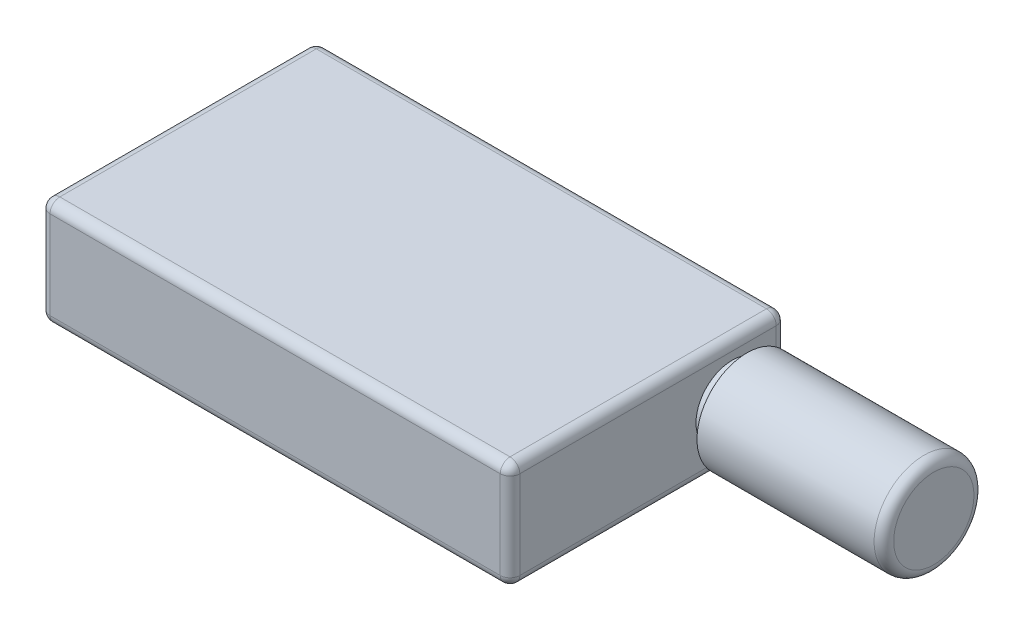
SolidWorks part; units mm, degrees
ref_plane "Front Plane" through (0, 0, 0) normal (0, 0, 1) x (1, 0, 0)
ref_plane "Top Plane" through (0, 0, 0) normal (0, 1, 0) x (1, 0, 0)
ref_plane "Right Plane" through (0, 0, 0) normal (1, 0, 0) x (0, 0, -1)
sketch "Sketch1" plane through (0, 0, 0) normal (0, 1, 0) x (1, 0, 0)
  line L1 (0, 0) -> (48, 0)
  line L2 (0, 0) -> (0, 28.2)
  line L3 (0, 28.2) -> (48, 28.2)
  line L4 (48, 0) -> (48, 28.2)
  dimension "D1" = 28.2
  dimension "D2" = 48
extrude "Boss-Extrude1" add sketch "Sketch1" along normal blind 11
sketch "Sketch2" plane through (48, 0, 0) normal (1, 0, 0) x (0, 0, -1)
  line L0 (28.2, 11) -> (28.2, 0) construction
  circle A0 centre (22.7, 5.5) radius 3.7
  point P5 (28.2, 5.5)
  dimension "D1" = 7.4
  dimension "D2" = 5.5
extrude "Boss-Extrude2" add sketch "Sketch2" along normal blind 1.5
sketch "Sketch3" plane through (49.5, 0, 0) normal (1, 0, 0) x (0, 0, -1)
  circle A0 centre (22.7, 5.5) radius 5.1
  dimension "D1" = 10.2
extrude "Boss-Extrude3" add sketch "Sketch3" along normal blind 19.1
fillet "Fillet1" radius 1 12 edges at (48, 0, -14.1) (48, 5.5, -28.2) (24, 0, -28.2) (0, 5.5, -28.2) (0, 0, -14.1) (0, 5.5, 0) (48, 5.5, 0) (24, 0, 0) (24, 11, -28.2) (48, 11, -14.1) (24, 11, 0) (0, 11, -14.1)
fillet "Fillet2" radius 1 1 edges at (68.6, 5.5, -27.8)
fillet "Fillet3" radius 1 1 edges at (49.5, 5.5, -26.4)
